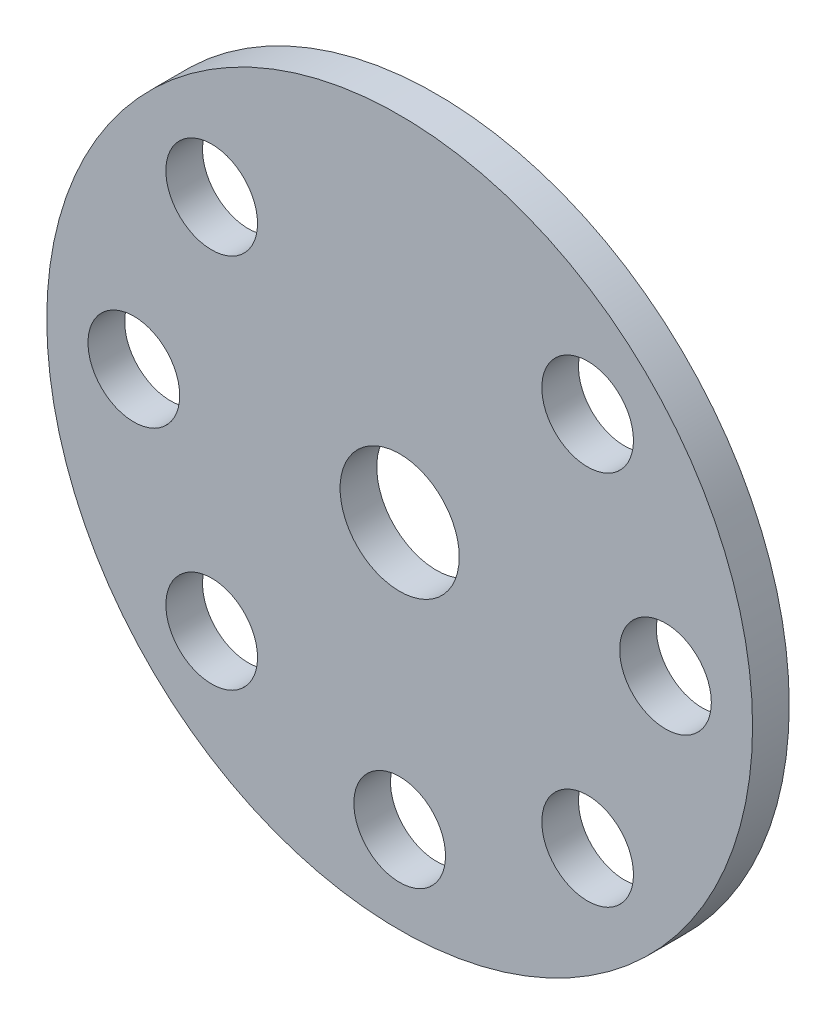
SolidWorks part; units mm, degrees
material "Ст 3 ГОСТ 380-2005"
ref_plane "Спереди" through (0, 0, 0) normal (0, 0, 1) x (1, 0, 0)
ref_plane "Сверху" through (0, 0, 0) normal (0, 1, 0) x (1, 0, 0)
ref_plane "Слева" through (0, 0, 0) normal (1, 0, 0) x (0, 0, -1)
sketch "Эскиз1" plane through (0, 0, 0) normal (0, 0, 1) x (1, 0, 0)
  circle A0 centre (0, 0) radius 19.25
  dimension "D1" = 38.5
extrude "Вытянуть1" add sketch "Эскиз1" along normal blind 2
hole_wizard "Зенковка для винта с полупотайной головкой M61" positions "Эскиз3" profile "Эскиз2" countersink size "M6" standard "ГОСТ"
sketch "Эскиз3" plane through (0, 0, 4) normal (0, 0, 1) x (1, 0, 0)
  circle A0 centre (0, 0) radius 18.25 construction
  point P0 (0, 0)
sketch "Эскиз2" plane through (0, 0, 4) normal (1, 0, 0) x (0, -1, 0)
  line L0 (0, 0) -> (0, 4)
  line L1 (0, 4) -> (3.2, 4)
  line L2 (3.2, 4) -> (3.2, 3)
  line L3 (3.2, 3) -> (6.2, 0)
  line L5 (6.2, 0) -> (0, 0)
  line L6 (-3.2, 3) -> (-6.2, 0) construction
  line L11 (0, -6.35) -> (0, 107.95) construction
  dimension "Диаметр сквозного отверстия" = 6.4
  dimension "Глубина сквозного отверстия" = 4
  dimension "Диаметр передней зенковки" = 12.4
  dimension "Угол передней зенковки" = 90
sketch "Эскиз4" plane through (0, 0, 2) normal (0, 0, 1) x (1, 0, 0)
  line L1 (0, 14.5) -> (-10.253, 10.253) construction
  line L2 (-10.253, 10.253) -> (-14.5, 0) construction
  line L3 (-14.5, 0) -> (-10.253, -10.253) construction
  line L4 (-10.253, -10.253) -> (0, -14.5) construction
  line L5 (0, -14.5) -> (10.253, -10.253) construction
  line L6 (10.253, -10.253) -> (14.5, 0) construction
  line L7 (14.5, 0) -> (10.253, 10.253) construction
  line L8 (10.253, 10.253) -> (0, 14.5) construction
  circle A0 centre (0, 0) radius 14.5 construction
  circle A1 centre (-10.253, 10.253) radius 2.5
  circle A2 centre (-14.5, 0) radius 2.5
  circle A3 centre (-10.253, -10.253) radius 2.5
  circle A4 centre (0, -14.5) radius 2.5
  circle A5 centre (10.253, -10.253) radius 2.5
  circle A6 centre (14.5, 0) radius 2.5
  circle A7 centre (10.253, 10.253) radius 2.5
  circle A8 centre (0, 0) radius 3.25
  dimension "D1" = 29
  dimension "D2" = 6.5
  dimension "D3" = 5
extrude "Вытянуть2" cut sketch "Эскиз4" against normal through all
